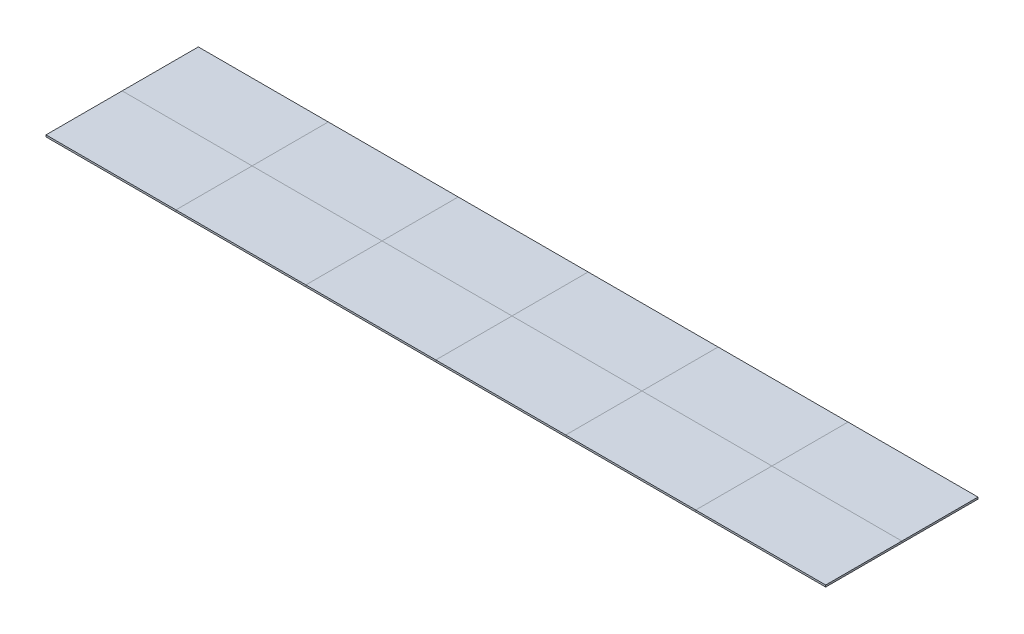
SolidWorks part; units mm, degrees
ref_plane "Front Plane" through (0, 0, 0) normal (0, 0, 1) x (1, 0, 0)
ref_plane "Top Plane" through (0, 0, 0) normal (0, 1, 0) x (1, 0, 0)
ref_plane "Right Plane" through (0, 0, 0) normal (1, 0, 0) x (0, 0, -1)
sketch "Sketch1" plane through (0, 0, 0) normal (0, 1, 0) x (1, 0, 0)
  line L4 (0, 0) -> (12026.9, 0)
  line L5 (12026.9, 0) -> (12026.9, 2349.5)
  line L6 (12026.9, 2349.5) -> (0, 2349.5)
  line L7 (0, 2349.5) -> (0, 0)
  line L8 (0, 0) -> (12026.9, 0)
  line L9 (12026.9, 0) -> (12026.9, 2349.5)
  line L10 (12026.9, 2349.5) -> (0, 2349.5)
  line L11 (0, 2349.5) -> (0, 0)
  dimension "D1" = 0
extrude "Boss-Extrude1" add sketch "Sketch1" against normal blind 27.94
sketch "Sketch3" plane through (0, 0, 0) normal (0, 1, 0) x (1, 0, 0)
  line L0 (0, 1174.75) -> (12026.9, 1174.75)
  line L1 (0, 2349.5) -> (0, 0) construction
  line L2 (12026.9, 0) -> (12026.9, 2349.5) construction
  line L3 (2004.4833, 0) -> (2004.4833, 2349.5)
  line L4 (12026.9, 2349.5) -> (0, 2349.5) construction
  line L5 (4008.9667, 0) -> (4008.9667, 2349.5)
  line L7 (10022.4167, 0) -> (10022.4167, 2349.5)
  line L8 (8017.9333, 0) -> (8017.9333, 2349.5)
  line L9 (6013.45, 0) -> (6013.45, 2349.5)
  point P11 (2004.4833, 1174.75)
  point P14 (4008.9667, 1174.75)
  point P20 (10022.4167, 1174.75)
  point P23 (8017.9333, 1174.75)
  point P27 (6013.45, 1174.75)
  dimension "D1" = 6013.45
  dimension "D2" = 2004.4833
  dimension "D3" = 2004.4833
  dimension "D4" = 2004.4833
  dimension "D5" = 2004.4833
split "Split1" trim tools "Sketch3" bodies to split 101 resulting bodies 102 103 104 105 107 108 109 110 114 115 116 117
equation "\"D2@Sketch3\"=\"D1@Sketch3\"/3"
equation "\"D3@Sketch3\"=\"D2@Sketch3\""
equation "\"D4@Sketch3\"=\"D2@Sketch3\""
equation "\"D5@Sketch3\"=\"D4@Sketch3\""
